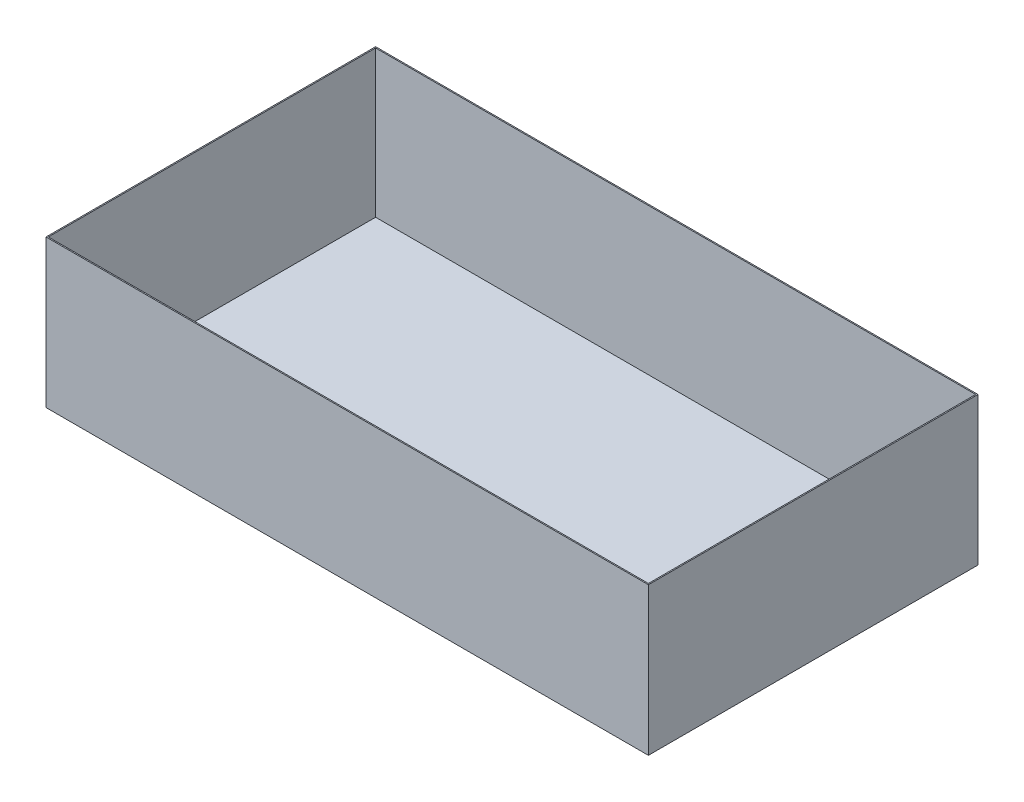
SolidWorks part; units mm, degrees
material "ABS PC"
ref_plane "Front Plane" through (0, 0, 0) normal (0, 0, 1) x (1, 0, 0)
ref_plane "Top Plane" through (0, 0, 0) normal (0, 1, 0) x (1, 0, 0)
ref_plane "Right Plane" through (0, 0, 0) normal (1, 0, 0) x (0, 0, -1)
sketch "Sketch1" plane through (0, 0, 0) normal (0, 1, 0) x (1, 0, 0)
  line L1 (-224.9762, 90.5803) -> (305.0238, 90.5803)
  line L2 (-224.9762, 90.5803) -> (-224.9762, -199.4197)
  line L3 (-224.9762, -199.4197) -> (305.0238, -199.4197)
  line L4 (305.0238, 90.5803) -> (305.0238, -199.4197)
  dimension "D1" = 530
  dimension "D2" = 290
extrude "Boss-Extrude1" add sketch "Sketch1" along normal blind 130
shell "Shell2" thickness 1
